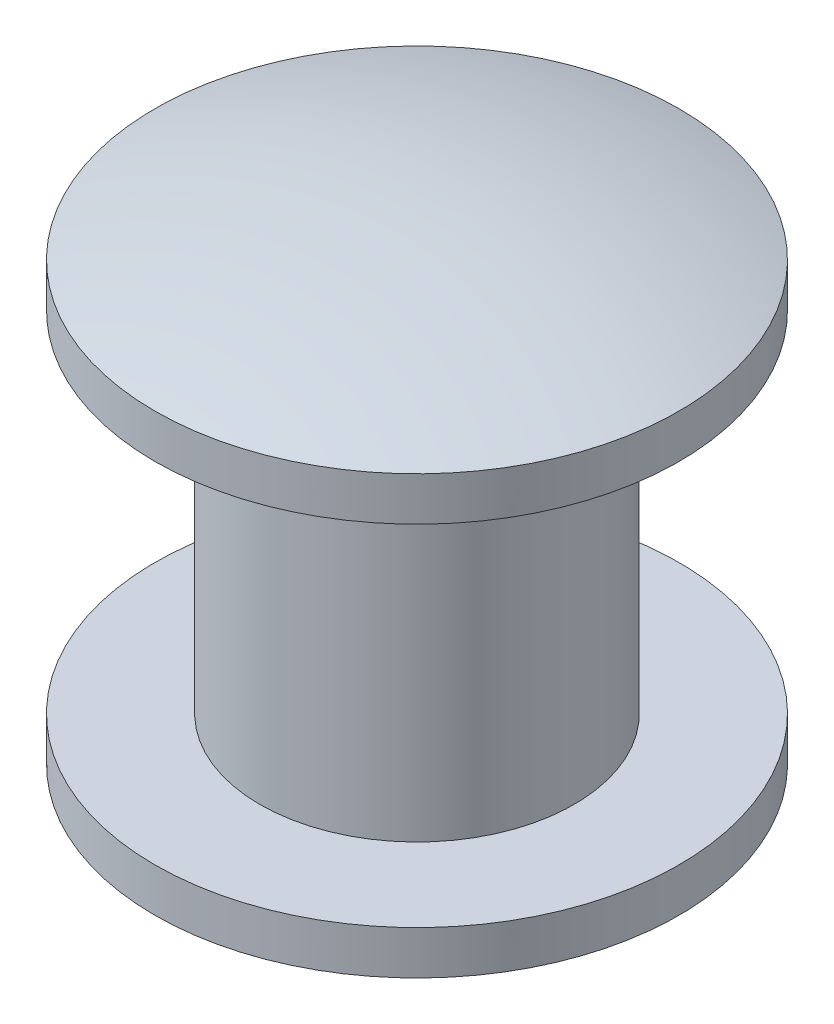
SolidWorks part; units mm, degrees
material "Plain Carbon Steel"
ref_plane "Front XY" through (0, 0, 0) normal (0, 0, 1) x (1, 0, 0)
ref_plane "Top XZ" through (0, 0, 0) normal (0, 1, 0) x (1, 0, 0)
ref_plane "Right YZ" through (0, 0, 0) normal (1, 0, 0) x (0, 0, -1)
sketch "Sketch1" plane through (0, 0, 0) normal (1, 0, 0) x (0, 0, -1)
  line L0 (0, 0) -> (0, -7.62)
  line L1 (3.81, -6.985) -> (3.81, -6.35)
  line L2 (3.81, -6.35) -> (2.286, -6.35)
  line L3 (2.286, -6.35) -> (2.286, -1.27)
  line L4 (2.286, -1.27) -> (3.81, -1.27)
  line L5 (3.81, -1.27) -> (3.81, -0.635)
  arc A0 (0, -7.62) -> (3.81, -6.985) centre (0, 4.1275) ccw
  arc A1 (0, 0) -> (3.81, -0.635) centre (0, -11.7475) cw
  dimension "D4" = 0.635
  dimension "D1" = 7.62
  dimension "D2" = 1.27
  dimension "D3" = 5.08
  dimension "D5" = 0.635
  dimension "D6" = 3.81
  dimension "D7" = 2.286
revolve "Revolve1" add sketch "Sketch1" angle 360 about L0
